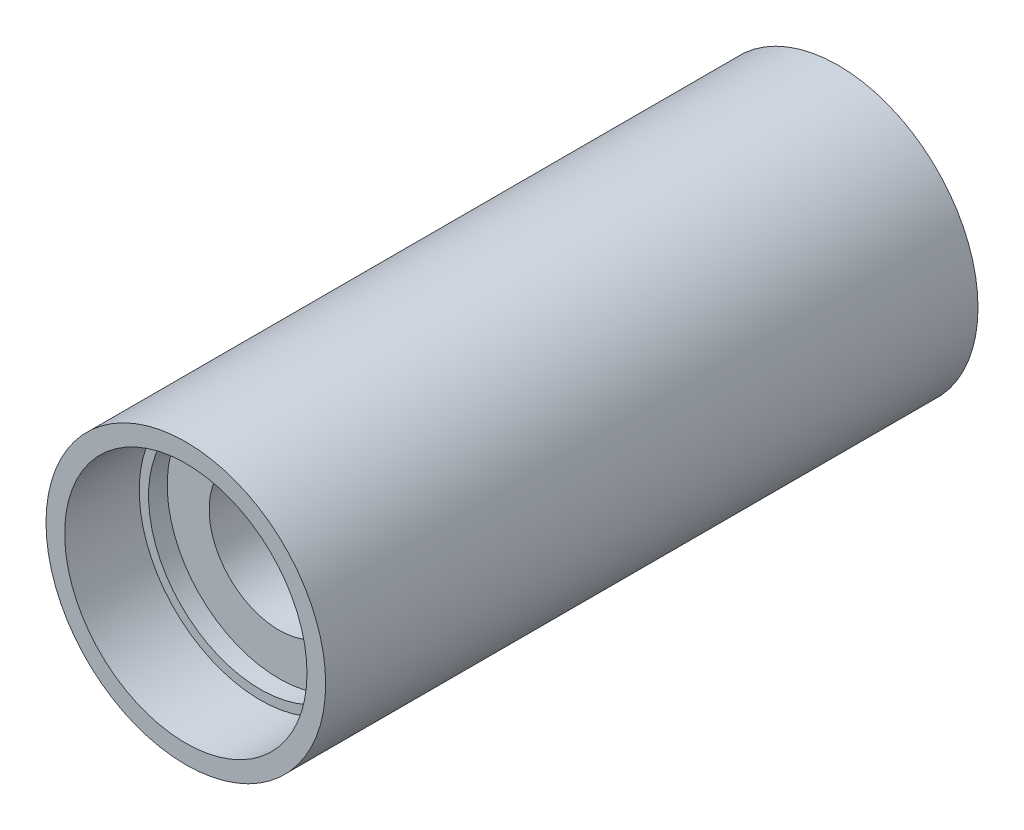
SolidWorks part; units mm, degrees
material "AISI 1020"
ref_plane "Спереди" through (0, 0, 0) normal (0, 0, 1) x (1, 0, 0)
ref_plane "Сверху" through (0, 0, 0) normal (0, 1, 0) x (1, 0, 0)
ref_plane "Справа" through (0, 0, 0) normal (1, 0, 0) x (0, 0, -1)
sketch "Эскиз1" plane through (0, 0, 0) normal (0, 1, 0) x (1, 0, 0)
  line L0 (15, 0) -> (7.5, 0) construction
  line L1 (15, -34.99) -> (15, 0) construction
  line L2 (13, -34.99) -> (15, -34.99) construction
  line L3 (13, -26.99) -> (13, -34.99) construction
  line L4 (12, -26.99) -> (13, -26.99) construction
  line L5 (12, -24.99) -> (12, -26.99) construction
  line L6 (7.5, -24.99) -> (12, -24.99) construction
  line L7 (7.5, 0) -> (7.5, -24.99) construction
  line L8 (15, 0) -> (7.5, 0)
  line L9 (15, -34.99) -> (15, 0)
  line L10 (13, -34.99) -> (15, -34.99)
  line L11 (13, -26.99) -> (13, -34.99)
  line L12 (12, -26.99) -> (13, -26.99)
  line L13 (12, -24.99) -> (12, -26.99)
  line L14 (7.5, -24.99) -> (12, -24.99)
  line L15 (7.5, 0) -> (7.5, -24.99)
  line L17 (0, -1005.293) -> (0, 48994.707) construction
revolve "Повернуть1" add sketch "Эскиз1" angle 360 about L17
mirror "Зеркальное отражение1" about plane through (15, 0, 0) normal (0, 0, -1) of bodies 103
